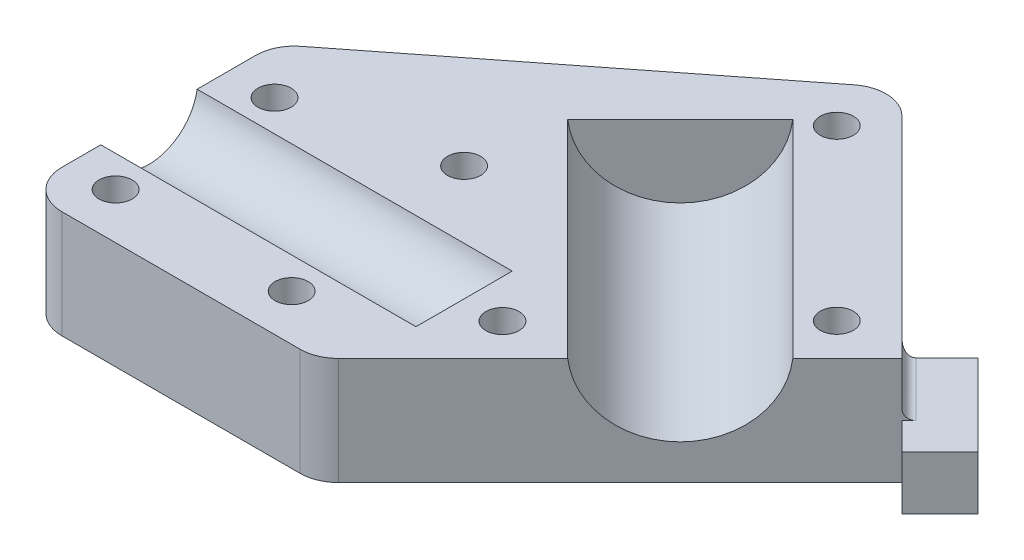
SolidWorks part; units mm, degrees
material "ABS"
ref_plane "前视基准面" through (0, 0, 0) normal (0, 0, 1) x (1, 0, 0)
ref_plane "上视基准面" through (0, 0, 0) normal (0, 1, 0) x (1, 0, 0)
ref_plane "右视基准面" through (0, 0, 0) normal (1, 0, 0) x (0, 0, -1)
ref_plane "基准面4" through (0, -15, 0) normal (0, -1, 0) x (1, 0, 0)
sketch "草图1" plane through (0, -15, 0) normal (0, -1, 0) x (1, 0, 0)
  line L0 (4.7435, -52.275) -> (35.2198, -21.7987)
  line L1 (35.2198, -21.7987) -> (-2.9289, 16.35)
  line L2 (-2.9289, 16.35) -> (-41.0289, 16.35)
  line L3 (-41.0289, 16.35) -> (-41.0289, -16.35)
  line L4 (-41.0289, -16.35) -> (4.7435, -52.275)
extrude "凸台-拉伸1" add sketch "草图1" against normal blind 14
sketch "草图2" plane through (0, -15, 0) normal (0, -1, 0) x (1, 0, 0)
  line L0 (43.705, -23.2129) -> (38.7553, -18.2632)
  line L1 (38.7553, -18.2632) -> (35.2198, -21.7987)
  line L2 (35.2198, -21.7987) -> (28.1487, -28.8698)
  line L3 (28.1487, -28.8698) -> (33.0984, -33.8195)
  line L4 (33.0984, -33.8195) -> (43.705, -23.2129)
extrude "凸台-拉伸2" add sketch "草图2" against normal blind 7
sketch "草图3" plane through (-41.0289, 0, 0) normal (-1, 0, 0) x (0, 0, 1)
  line L0 (6.2708, -1) -> (-6.2708, -1)
  arc A0 (-6.2708, -1) -> (6.2708, -1) centre (0, 0) ccw
extrude "切除-拉伸1" cut sketch "草图3" against normal blind 41.0289
sketch "草图4" plane through (6.7105, 0, 6.7105) normal (0.7071, 0, 0.7071) x (0.7071, 0, -0.7071)
  line L0 (30.27, -1) -> (9.5383, -1)
  arc A0 (9.5383, -1) -> (30.27, -1) centre (19.9041, 0) ccw
extrude "切除-拉伸2" cut sketch "草图4" against normal blind 38.1
ref_plane "基准面5" through (0, -12, 0) normal (0, -1, 0) x (1, 0, 0)
ref_plane "基准面6" through (0, -17, 0) normal (0, 1, 0) x (1, 0, 0)
hole_wizard "M4 间隙孔1" positions "草图16" profile "草图15" hole size "M4" standard "ANSI Metric"
sketch "草图16" plane through (0, -15, 0) normal (0, -1, 0) x (-1, 0, 0)
  point P0 (35.0289, -10.35)
  point P1 (-5, 0)
  point P2 (15, 15)
  point P3 (12.103, -10.35)
  point P4 (35.0289, 10.35)
  point P5 (-4.7435, 43.7897)
  point P6 (-26.7345, 21.7987)
sketch "草图15" plane through (-35.0289, -15, 10.35) normal (1, 0, 0) x (0, 0, -1)
  line L0 (0, 0) -> (0, 14)
  line L1 (0, 14) -> (2.159, 14)
  line L2 (2.159, 14) -> (2.159, 0)
  line L5 (2.159, 0) -> (0, 0)
  line L11 (0, -6.35) -> (0, 107.95) construction
  dimension "通孔孔直径" = 4.318
  dimension "通孔孔深度" = 14
fillet "圆角1" radius 5 4 edges at (-41.0289, -8, 16.35) (-2.9289, -8, 16.35) (-41.0289, -8, -16.35) (4.7435, -8, -52.275)
fillet "圆角3" radius 1.27 1 edges at (31.6842, -8, -25.3342)
fillet "圆角4" radius 1.27 1 edges at (28.1487, -10.865, -28.8698)
